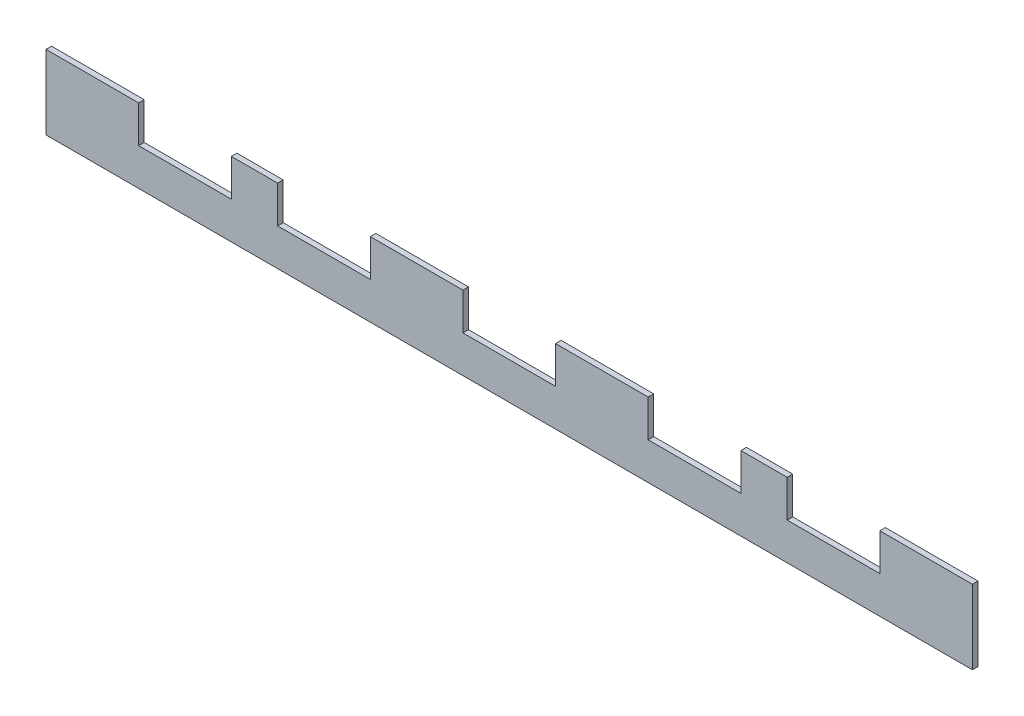
SolidWorks part; units mm, degrees
material "PMMA"
ref_plane "Front Plane" through (0, 0, 0) normal (0, 0, 1) x (1, 0, 0)
ref_plane "Top Plane" through (0, 0, 0) normal (0, 1, 0) x (1, 0, 0)
ref_plane "Right Plane" through (0, 0, 0) normal (1, 0, 0) x (0, 0, -1)
sketch "Sketch1" plane through (0, 0, 0) normal (0, 0, 1) x (1, 0, 0)
  line L1 (0, 0) -> (500, 0)
  line L2 (0, 0) -> (0, 40)
  line L3 (0, 40) -> (500, 40)
  line L4 (500, 0) -> (500, 40)
  dimension "D1" = 500
  dimension "D2" = 40
extrude "Boss-Extrude1" add sketch "Sketch1" along normal blind 3
sketch "Sketch3" plane through (0, 0, 3) normal (0, 0, 1) x (1, 0, 0)
  line L0 (500, 40) -> (0, 40) construction
  line L1 (50, 40) -> (100, 40)
  line L2 (50, 40) -> (50, 20)
  line L3 (50, 20) -> (100, 20)
  line L5 (0, 40) -> (0, 0) construction
  line L7 (100, 40) -> (100, 20)
  line L10 (125, 40) -> (175, 40)
  line L11 (125, 40) -> (125, 20)
  line L12 (125, 20) -> (175, 20)
  line L13 (175, 40) -> (175, 20)
  line L14 (225, 40) -> (275, 40)
  line L15 (225, 40) -> (225, 20)
  line L16 (225, 20) -> (275, 20)
  line L17 (275, 40) -> (275, 20)
  line L18 (400, 40) -> (450, 40)
  line L19 (400, 40) -> (400, 20)
  line L20 (400, 20) -> (450, 20)
  line L21 (450, 40) -> (450, 20)
  line L22 (500, 0) -> (500, 40) construction
  line L24 (325, 40) -> (375, 40)
  line L25 (325, 40) -> (325, 20)
  line L26 (325, 20) -> (375, 20)
  line L27 (375, 40) -> (375, 20)
  point P6 (100, 30)
  dimension "D1" = 50
  dimension "D2" = 25
  dimension "D3" = 50
  dimension "D4" = 50
  dimension "D5" = 50
  dimension "D6" = 20
  dimension "D7" = 50
  dimension "D8" = 50
  dimension "D9" = 50
  dimension "D10" = 50
  dimension "D11" = 50
extrude "Cut-Extrude2" cut sketch "Sketch3" against normal through all
